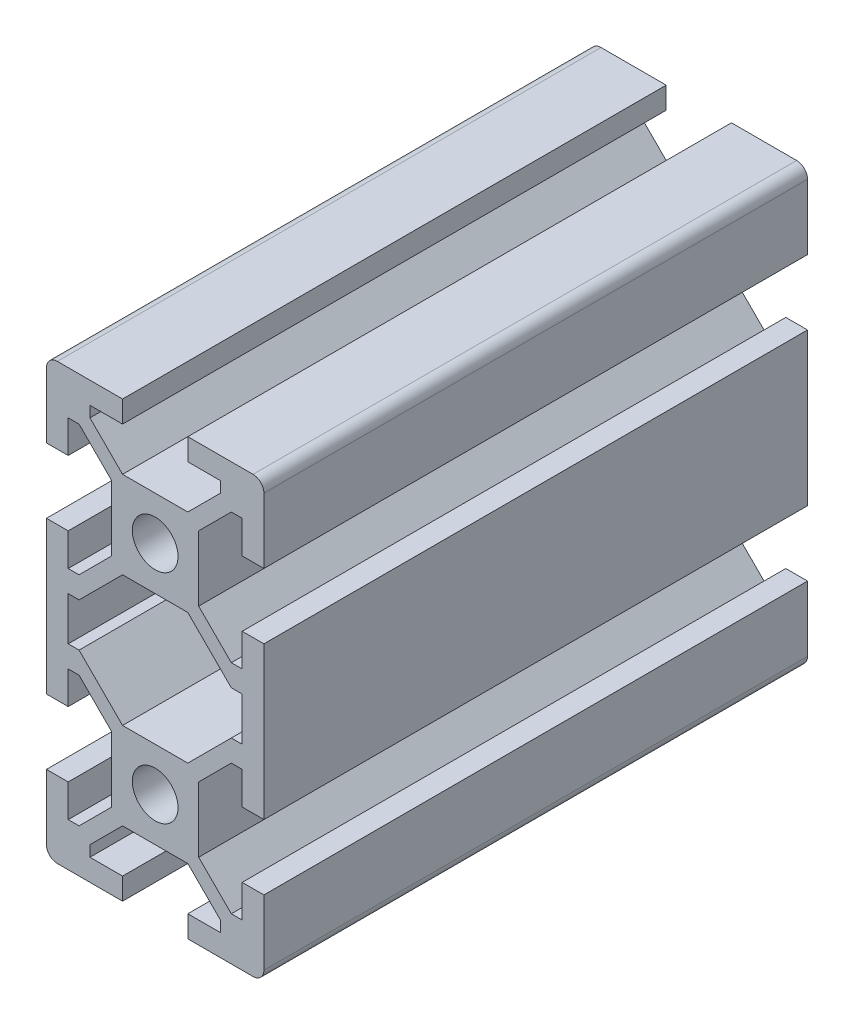
SolidWorks part; units mm, degrees
material "6063-O, Barra estrusa (SS)"
ref_plane "Piano frontale" through (0, 0, 0) normal (0, 0, 1) x (1, 0, 0)
ref_plane "Piano superiore" through (0, 0, 0) normal (0, 1, 0) x (1, 0, 0)
ref_plane "Piano destro" through (0, 0, 0) normal (1, 0, 0) x (0, 0, -1)
other "Lunghezza"
other "Lunghezze"
sketch "Schizzo1" plane through (0, 0, 0) normal (0, 0, 1) x (1, 0, 0)
  line L0 (-6, 18) -> (6, 18) construction
  line L1 (10, 20) -> (-10, 20) construction
  line L2 (10, 20) -> (10, -20) construction
  line L3 (-8, 4) -> (-8, -4) construction
  line L4 (-10, 20) -> (-10, -20) construction
  line L5 (10, 20) -> (-10, 0) construction
  line L6 (10, 0) -> (-10, 20) construction
  line L7 (-3, 14) -> (3, 14) construction
  line L8 (-3, 32.3825) -> (-3, 22.2883) construction
  line L9 (0, 33.8953) -> (0, -6.3729) construction
  line L10 (3, 32.3825) -> (3, 22.2883) construction
  line L11 (-6, 11.8152) -> (-6, 23.4013) construction
  line L12 (6, 10.4596) -> (6, 33.4013) construction
  line L13 (-3, 14) -> (-9, 20) construction
  line L14 (-10, 20) -> (-3, 20)
  line L15 (-3, 20) -> (-3, 18)
  line L16 (-3, 18) -> (-6, 18)
  line L17 (-6, 18) -> (-6, 17)
  line L18 (-6, 17) -> (-3, 14)
  line L19 (-3, 14) -> (3, 14)
  line L20 (3, 14) -> (9, 20) construction
  line L21 (3, 14) -> (6, 17)
  line L22 (6, 17) -> (6, 18)
  line L23 (6, 18) -> (3, 18)
  line L24 (3, 18) -> (3, 20)
  line L25 (3, 20) -> (10, 20)
  line L26 (10, 20) -> (10, 13)
  line L27 (10, 13) -> (8, 13)
  line L28 (8, 13) -> (8, 16)
  line L29 (8, 16) -> (7, 16)
  line L30 (7, 16) -> (4, 13)
  line L31 (4, 13) -> (4, 7)
  line L32 (4, 7) -> (7, 4)
  line L33 (8, 4) -> (8, 7)
  line L34 (7, 4) -> (8, 4)
  line L35 (8, 7) -> (10, 7)
  line L36 (10, 7) -> (10, 0)
  line L37 (8, 4) -> (8, -4) construction
  line L38 (-7, 4) -> (-7, -4) construction
  line L39 (7, 4) -> (7, -4) construction
  line L40 (3, -6) -> (7, -2)
  line L41 (-3, 6) -> (-7, 2)
  line L42 (3, 6) -> (-3, 6)
  line L43 (3, 6) -> (7, 2)
  line L44 (-3, -6) -> (-7, -2)
  line L45 (-7, -2) -> (-8, -2)
  line L46 (-8, -2) -> (-8, 2)
  line L47 (-8, 2) -> (-7, 2)
  line L48 (-10, 0) -> (-10, 7)
  line L49 (-10, 7) -> (-8, 7)
  line L50 (-8, 7) -> (-8, 4)
  line L51 (-8, 4) -> (-7, 4)
  line L52 (-7, 4) -> (-4, 7)
  line L53 (-4, 7) -> (-4, 13)
  line L54 (-4, 13) -> (-7, 16)
  line L55 (-8, 16) -> (-8, 13)
  line L56 (-7, 16) -> (-8, 16)
  line L57 (-8, 13) -> (-10, 13)
  line L58 (-10, 13) -> (-10, 20)
  line L59 (-19.9461, 0) -> (34.5024, 0) construction
  line L60 (3, -14) -> (9, -20) construction
  line L61 (-3, -14) -> (-9, -20) construction
  line L62 (-3, -14) -> (3, -14) construction
  line L63 (10, 0) -> (-10, -20) construction
  line L64 (10, -20) -> (-10, 0) construction
  line L65 (10, -20) -> (-10, -20) construction
  line L66 (-6, -18) -> (6, -18) construction
  line L67 (-10, -13) -> (-10, -20)
  line L68 (-8, -13) -> (-10, -13)
  line L69 (-7, -16) -> (-8, -16)
  line L70 (-8, -16) -> (-8, -13)
  line L71 (-4, -13) -> (-7, -16)
  line L72 (-4, -7) -> (-4, -13)
  line L73 (-7, -4) -> (-4, -7)
  line L74 (-8, -4) -> (-7, -4)
  line L75 (-8, -7) -> (-8, -4)
  line L76 (-10, -7) -> (-8, -7)
  line L77 (-10, 0) -> (-10, -7)
  line L78 (7, -2) -> (8, -2)
  line L79 (8, -2) -> (8, 2)
  line L80 (8, 2) -> (7, 2)
  line L81 (3, -6) -> (-3, -6)
  line L85 (10, -7) -> (10, 0)
  line L86 (8, -7) -> (10, -7)
  line L87 (7, -4) -> (8, -4)
  line L88 (8, -4) -> (8, -7)
  line L89 (4, -7) -> (7, -4)
  line L90 (4, -13) -> (4, -7)
  line L91 (7, -16) -> (4, -13)
  line L92 (8, -16) -> (7, -16)
  line L93 (8, -13) -> (8, -16)
  line L94 (10, -13) -> (8, -13)
  line L95 (10, -20) -> (10, -13)
  line L96 (3, -20) -> (10, -20)
  line L97 (3, -18) -> (3, -20)
  line L98 (6, -18) -> (3, -18)
  line L99 (6, -17) -> (6, -18)
  line L100 (3, -14) -> (6, -17)
  line L101 (-3, -14) -> (3, -14)
  line L102 (-6, -17) -> (-3, -14)
  line L103 (-6, -18) -> (-6, -17)
  line L104 (-3, -18) -> (-6, -18)
  line L105 (-3, -20) -> (-3, -18)
  line L106 (-10, -20) -> (-3, -20)
  line L107 (-3, 0) -> (-10, 0) [skipped]
  line L108 (-3, 0) -> (-3, -2) [skipped]
  line L109 (3, 0) -> (3, 2) [skipped]
  line L110 (10, 0) -> (3, 0) [skipped]
  line L111 (-6, 3) -> (-6, 2) [skipped]
  line L112 (-6, 2) -> (-3, 2) [skipped]
  line L113 (3, 2) -> (6, 2) [skipped]
  line L114 (6, 2) -> (6, 3) [skipped]
  line L115 (-3, 6) -> (-6, 3) [skipped]
  line L116 (6, 3) -> (3, 6) [skipped]
  circle A0 centre (0, 10) radius 2.1
  circle A1 centre (0, -10) radius 2.1
  point P0 (0, 10)
  point P5 (0, 14)
  point P11 (0, 18)
  point P71 (0, 10)
  dimension "D8" = 4.2
  dimension "D2" = 20
  dimension "D3" = 2
  dimension "D4" = 4
  dimension "D5" = 6
  dimension "D6" = 12
  dimension "D7" = 4
  dimension "D9" = 6
  dimension "D10" = 3
  dimension "D11" = 40
extrude "Estrusione-Estrusione1" add sketch "Schizzo1" along normal blind 50 contours L67 L106 L105 L104 L103 L102 L101 L100 L99 L98 L97 L96 L95 L94 L93 L92 L91 L90 L89 L87 L88 L86 L85 L36 L35 L33 L34 L32 L31 L30 L29 L28 L27 L26 L25 L24 L23 L22 L21 L19 L18 L17 L16 L15 L14 L58 L57 L55 L56 L54 L53
fillet "Raccordo1" radius 1 4 edges at (-10, -20, 25) (10, -20, 25) (-10, 20, 25) (10, 20, 25)
